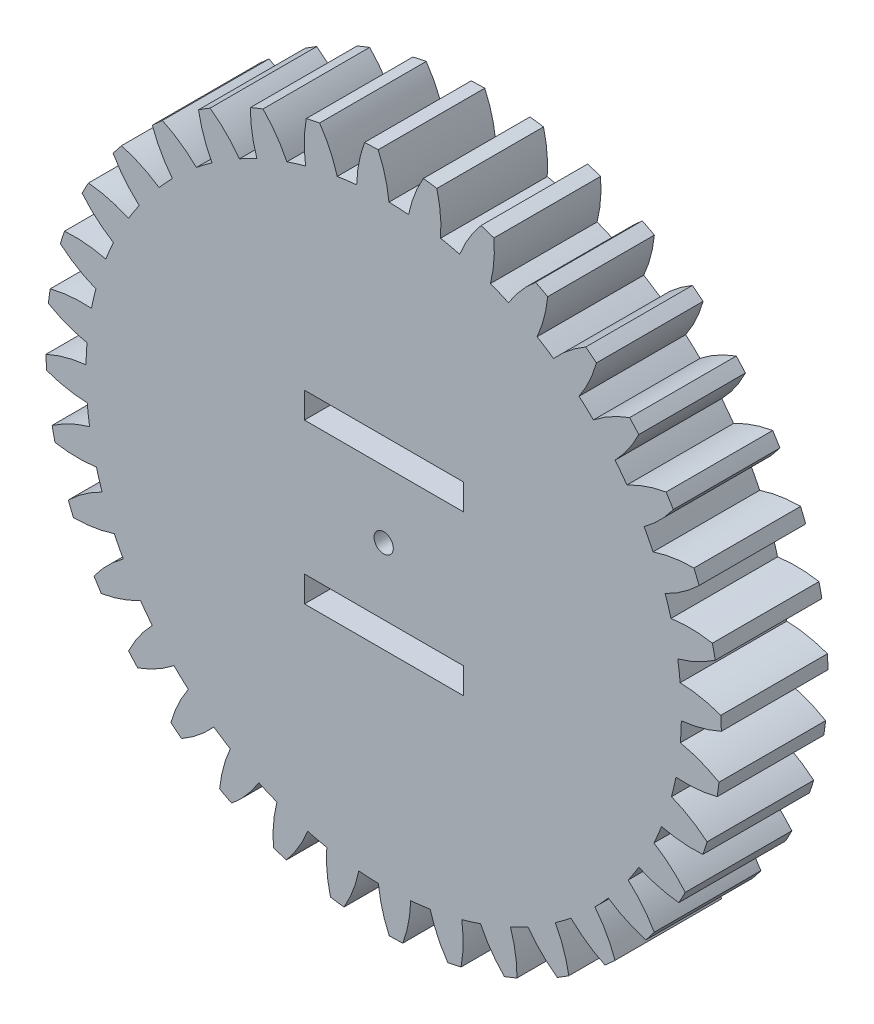
SolidWorks part; units mm, degrees
ref_plane "Front Plane" through (0, 0, 0) normal (0, 0, 1) x (1, 0, 0)
ref_plane "Top Plane" through (0, 0, 0) normal (0, 1, 0) x (1, 0, 0)
ref_plane "Right Plane" through (0, 0, 0) normal (1, 0, 0) x (0, 0, -1)
ref_plane "Plane1" through (0, 0, 0) normal (0, 0, -1) x (-1, 0, 0)
sketch "Sketch1" plane through (0, 0, 0) normal (0, 0, -1) x (-1, 0, 0)
  circle A0 centre (0, 0) radius 0.3969
  arc A1 (-79.4291, -12.6704) -> (-69.5997, -13.5532) centre (-71.8238, 16.8455) ccw
  arc A2 (-69.5997, -13.5532) -> (-68.5577, -18.1012) centre (0, 0) ccw
  arc A3 (-68.5577, -18.1012) -> (-77.0222, -23.1754) centre (-57.3249, -46.4358) ccw
  arc A4 (-77.0222, -23.1754) -> (-76.0222, -26.2707) centre (0, 0) ccw
  arc A5 (-76.0222, -26.2707) -> (-66.1889, -25.4332) centre (-73.6579, 4.1175) ccw
  arc A6 (-66.1889, -25.4332) -> (-64.3729, -29.7311) centre (0, 0) ccw
  arc A7 (-64.3729, -29.7311) -> (-71.8277, -36.1981) centre (-48.3905, -55.6847) ccw
  arc A8 (-71.8277, -36.1981) -> (-70.3054, -39.0727) centre (0, 0) ccw
  arc A9 (-70.3054, -39.0727) -> (-60.7669, -36.5404) centre (-73.2538, -8.7356) ccw
  arc A10 (-60.7669, -36.5404) -> (-58.2322, -40.4576) centre (0, 0) ccw
  arc A11 (-58.2322, -40.4576) -> (-64.4507, -48.1209) centre (-37.9858, -63.2417) ccw
  arc A12 (-64.4507, -48.1209) -> (-62.4524, -50.6875) centre (0, 0) ccw
  arc A13 (-62.4524, -50.6875) -> (-53.4985, -46.5373) centre (-70.624, -21.3233) ccw
  arc A14 (-53.4985, -46.5373) -> (-50.3221, -49.9549) centre (0, 0) ccw
  arc A15 (-50.3221, -49.9549) -> (-55.1155, -58.5816) centre (-26.4269, -68.8771) ccw
  arc A16 (-55.1155, -58.5816) -> (-52.7018, -60.7621) centre (0, 0) ccw
  arc A17 (-52.7018, -60.7621) -> (-44.6046, -55.1202) centre (-65.8483, -33.2631) ccw
  arc A18 (-44.6046, -55.1202) -> (-40.8831, -57.9343) centre (0, 0) ccw
  arc A19 (-40.8831, -57.9343) -> (-44.1056, -67.2623) centre (-14.065, -72.4197) ccw
  arc A20 (-44.1056, -67.2623) -> (-41.3499, -68.9906) centre (0, 0) ccw
  arc A21 (-41.3499, -68.9906) -> (-34.3555, -62.0283) centre (-59.0719, -44.1922) ccw
  arc A22 (-34.3555, -62.0283) -> (-30.2018, -64.1535) centre (0, 0) ccw
  arc A23 (-30.2018, -64.1535) -> (-31.7555, -73.8993) centre (-1.2758, -73.7618) ccw
  arc A24 (-31.7555, -73.8993) -> (-28.7416, -75.1228) centre (0, 0) ccw
  arc A25 (-28.7416, -75.1228) -> (-23.0624, -67.0517) centre (-50.5006, -53.7785) ccw
  arc A26 (-23.0624, -67.0517) -> (-18.6028, -68.4233) centre (0, 0) ccw
  arc A27 (-18.6028, -68.4233) -> (-18.4406, -78.2909) centre (11.5522, -72.8628) ccw
  arc A28 (-18.4406, -78.2909) -> (-15.26, -78.9725) centre (0, 0) ccw
  arc A29 (-15.26, -78.9725) -> (-11.0686, -70.0378) centre (-40.3948, -61.7308) ccw
  arc A30 (-11.0686, -70.0378) -> (-6.4386, -70.6141) centre (0, 0) ccw
  arc A31 (-6.4386, -70.6141) -> (-4.5654, -80.3037) centre (24.0291, -69.7498) ccw
  arc A32 (-4.5654, -80.3037) -> (-1.3148, -80.4226) centre (0, 0) ccw
  arc A33 (-1.3148, -80.4226) -> (1.2615, -70.8958) centre (-29.0617, -67.8075) ccw
  arc A34 (1.2615, -70.8958) -> (5.9212, -70.6594) centre (0, 0) ccw
  arc A35 (5.9212, -70.6594) -> (9.4486, -79.8764) centre (35.776, -64.5175) ccw
  arc A36 (9.4486, -79.8764) -> (12.6704, -79.4291) centre (0, 0) ccw
  arc A37 (12.6704, -79.4291) -> (13.5532, -69.5997) centre (-16.8455, -71.8238) ccw
  arc A38 (13.5532, -69.5997) -> (18.1012, -68.5577) centre (0, 0) ccw
  arc A39 (18.1012, -68.5577) -> (23.1754, -77.0222) centre (46.4358, -57.3249) ccw
  arc A40 (23.1754, -77.0222) -> (26.2707, -76.0222) centre (0, 0) ccw
  arc A41 (26.2707, -76.0222) -> (25.4332, -66.1889) centre (-4.1175, -73.6579) ccw
  arc A42 (25.4332, -66.1889) -> (29.7311, -64.3729) centre (0, 0) ccw
  arc A43 (29.7311, -64.3729) -> (36.1981, -71.8277) centre (55.6847, -48.3905) ccw
  arc A44 (36.1981, -71.8277) -> (39.0727, -70.3054) centre (0, 0) ccw
  arc A45 (39.0727, -70.3054) -> (36.5404, -60.7669) centre (8.7356, -73.2538) ccw
  arc A46 (36.5404, -60.7669) -> (40.4576, -58.2322) centre (0, 0) ccw
  arc A47 (40.4576, -58.2322) -> (48.1209, -64.4507) centre (63.2417, -37.9858) ccw
  arc A48 (48.1209, -64.4507) -> (50.6875, -62.4524) centre (0, 0) ccw
  arc A49 (50.6875, -62.4524) -> (46.5373, -53.4985) centre (21.3233, -70.624) ccw
  arc A50 (46.5373, -53.4985) -> (49.9549, -50.3221) centre (0, 0) ccw
  arc A51 (49.9549, -50.3221) -> (58.5816, -55.1155) centre (68.8771, -26.4269) ccw
  arc A52 (58.5816, -55.1155) -> (60.7621, -52.7018) centre (0, 0) ccw
  arc A53 (60.7621, -52.7018) -> (55.1202, -44.6046) centre (33.2631, -65.8483) ccw
  arc A54 (55.1202, -44.6046) -> (57.9343, -40.8831) centre (0, 0) ccw
  arc A55 (57.9343, -40.8831) -> (67.2623, -44.1056) centre (72.4197, -14.065) ccw
  arc A56 (67.2623, -44.1056) -> (68.9906, -41.3499) centre (0, 0) ccw
  arc A57 (68.9906, -41.3499) -> (62.0283, -34.3555) centre (44.1922, -59.0719) ccw
  arc A58 (62.0283, -34.3555) -> (64.1535, -30.2018) centre (0, 0) ccw
  arc A59 (64.1535, -30.2018) -> (73.8993, -31.7555) centre (73.7618, -1.2758) ccw
  arc A60 (73.8993, -31.7555) -> (75.1228, -28.7416) centre (0, 0) ccw
  arc A61 (75.1228, -28.7416) -> (67.0517, -23.0624) centre (53.7785, -50.5006) ccw
  arc A62 (67.0517, -23.0624) -> (68.4233, -18.6028) centre (0, 0) ccw
  arc A63 (68.4233, -18.6028) -> (78.2909, -18.4406) centre (72.8628, 11.5522) ccw
  arc A64 (78.2909, -18.4406) -> (78.9725, -15.26) centre (0, 0) ccw
  arc A65 (78.9725, -15.26) -> (70.0378, -11.0686) centre (61.7308, -40.3948) ccw
  arc A66 (70.0378, -11.0686) -> (70.6141, -6.4386) centre (0, 0) ccw
  arc A67 (70.6141, -6.4386) -> (80.3037, -4.5654) centre (69.7498, 24.0291) ccw
  arc A68 (80.3037, -4.5654) -> (80.4226, -1.3148) centre (0, 0) ccw
  arc A69 (80.4226, -1.3148) -> (70.8958, 1.2615) centre (67.8075, -29.0617) ccw
  arc A70 (70.8958, 1.2615) -> (70.6594, 5.9212) centre (0, 0) ccw
  arc A71 (70.6594, 5.9212) -> (79.8764, 9.4486) centre (64.5175, 35.776) ccw
  arc A72 (79.8764, 9.4486) -> (79.4291, 12.6704) centre (0, 0) ccw
  arc A73 (79.4291, 12.6704) -> (69.5997, 13.5532) centre (71.8238, -16.8455) ccw
  arc A74 (69.5997, 13.5532) -> (68.5577, 18.1012) centre (0, 0) ccw
  arc A75 (68.5577, 18.1012) -> (77.0222, 23.1754) centre (57.3249, 46.4358) ccw
  arc A76 (77.0222, 23.1754) -> (76.0222, 26.2707) centre (0, 0) ccw
  arc A77 (76.0222, 26.2707) -> (66.1889, 25.4332) centre (73.6579, -4.1175) ccw
  arc A78 (66.1889, 25.4332) -> (64.3729, 29.7311) centre (0, 0) ccw
  arc A79 (64.3729, 29.7311) -> (71.8277, 36.1981) centre (48.3905, 55.6847) ccw
  arc A80 (71.8277, 36.1981) -> (70.3054, 39.0727) centre (0, 0) ccw
  arc A81 (70.3054, 39.0727) -> (60.7669, 36.5404) centre (73.2538, 8.7356) ccw
  arc A82 (60.7669, 36.5404) -> (58.2322, 40.4576) centre (0, 0) ccw
  arc A83 (58.2322, 40.4576) -> (64.4507, 48.1209) centre (37.9858, 63.2417) ccw
  arc A84 (64.4507, 48.1209) -> (62.4524, 50.6875) centre (0, 0) ccw
  arc A85 (62.4524, 50.6875) -> (53.4985, 46.5373) centre (70.624, 21.3233) ccw
  arc A86 (53.4985, 46.5373) -> (50.3221, 49.9549) centre (0, 0) ccw
  arc A87 (50.3221, 49.9549) -> (55.1155, 58.5816) centre (26.4269, 68.8771) ccw
  arc A88 (55.1155, 58.5816) -> (52.7018, 60.7621) centre (0, 0) ccw
  arc A89 (52.7018, 60.7621) -> (44.6046, 55.1202) centre (65.8483, 33.2631) ccw
  arc A90 (44.6046, 55.1202) -> (40.8831, 57.9343) centre (0, 0) ccw
  arc A91 (40.8831, 57.9343) -> (44.1056, 67.2623) centre (14.065, 72.4197) ccw
  arc A92 (44.1056, 67.2623) -> (41.3499, 68.9906) centre (0, 0) ccw
  arc A93 (41.3499, 68.9906) -> (34.3555, 62.0283) centre (59.0719, 44.1922) ccw
  arc A94 (34.3555, 62.0283) -> (30.2018, 64.1535) centre (0, 0) ccw
  arc A95 (30.2018, 64.1535) -> (31.7555, 73.8993) centre (1.2758, 73.7618) ccw
  arc A96 (31.7555, 73.8993) -> (28.7416, 75.1228) centre (0, 0) ccw
  arc A97 (28.7416, 75.1228) -> (23.0624, 67.0517) centre (50.5006, 53.7785) ccw
  arc A98 (23.0624, 67.0517) -> (18.6028, 68.4233) centre (0, 0) ccw
  arc A99 (18.6028, 68.4233) -> (18.4406, 78.2909) centre (-11.5522, 72.8628) ccw
  arc A100 (18.4406, 78.2909) -> (15.26, 78.9725) centre (0, 0) ccw
  arc A101 (15.26, 78.9725) -> (11.0686, 70.0378) centre (40.3948, 61.7308) ccw
  arc A102 (11.0686, 70.0378) -> (6.4386, 70.6141) centre (0, 0) ccw
  arc A103 (6.4386, 70.6141) -> (4.5654, 80.3037) centre (-24.0291, 69.7498) ccw
  arc A104 (4.5654, 80.3037) -> (1.3148, 80.4226) centre (0, 0) ccw
  arc A105 (1.3148, 80.4226) -> (-1.2615, 70.8958) centre (29.0617, 67.8075) ccw
  arc A106 (-1.2615, 70.8958) -> (-5.9212, 70.6594) centre (0, 0) ccw
  arc A107 (-5.9212, 70.6594) -> (-9.4486, 79.8764) centre (-35.776, 64.5175) ccw
  arc A108 (-9.4486, 79.8764) -> (-12.6704, 79.4291) centre (0, 0) ccw
  arc A109 (-12.6704, 79.4291) -> (-13.5532, 69.5997) centre (16.8455, 71.8238) ccw
  arc A110 (-13.5532, 69.5997) -> (-18.1012, 68.5577) centre (0, 0) ccw
  arc A111 (-18.1012, 68.5577) -> (-23.1754, 77.0222) centre (-46.4358, 57.3249) ccw
  arc A112 (-23.1754, 77.0222) -> (-26.2707, 76.0222) centre (0, 0) ccw
  arc A113 (-26.2707, 76.0222) -> (-25.4332, 66.1889) centre (4.1175, 73.6579) ccw
  arc A114 (-25.4332, 66.1889) -> (-29.7311, 64.3729) centre (0, 0) ccw
  arc A115 (-29.7311, 64.3729) -> (-36.1981, 71.8277) centre (-55.6847, 48.3905) ccw
  arc A116 (-36.1981, 71.8277) -> (-39.0727, 70.3054) centre (0, 0) ccw
  arc A117 (-39.0727, 70.3054) -> (-36.5404, 60.7669) centre (-8.7356, 73.2538) ccw
  arc A118 (-36.5404, 60.7669) -> (-40.4576, 58.2322) centre (0, 0) ccw
  arc A119 (-40.4576, 58.2322) -> (-48.1209, 64.4507) centre (-63.2417, 37.9858) ccw
  arc A120 (-48.1209, 64.4507) -> (-50.6875, 62.4524) centre (0, 0) ccw
  arc A121 (-50.6875, 62.4524) -> (-46.5373, 53.4985) centre (-21.3233, 70.624) ccw
  arc A122 (-46.5373, 53.4985) -> (-49.9549, 50.3221) centre (0, 0) ccw
  arc A123 (-49.9549, 50.3221) -> (-58.5816, 55.1155) centre (-68.8771, 26.4269) ccw
  arc A124 (-58.5816, 55.1155) -> (-60.7621, 52.7018) centre (0, 0) ccw
  arc A125 (-60.7621, 52.7018) -> (-55.1202, 44.6046) centre (-33.2631, 65.8483) ccw
  arc A126 (-55.1202, 44.6046) -> (-57.9343, 40.8831) centre (0, 0) ccw
  arc A127 (-57.9343, 40.8831) -> (-67.2623, 44.1056) centre (-72.4197, 14.065) ccw
  arc A128 (-67.2623, 44.1056) -> (-68.9906, 41.3499) centre (0, 0) ccw
  arc A129 (-68.9906, 41.3499) -> (-62.0283, 34.3555) centre (-44.1922, 59.0719) ccw
  arc A130 (-62.0283, 34.3555) -> (-64.1535, 30.2018) centre (0, 0) ccw
  arc A131 (-64.1535, 30.2018) -> (-73.8993, 31.7555) centre (-73.7618, 1.2758) ccw
  arc A132 (-73.8993, 31.7555) -> (-75.1228, 28.7416) centre (0, 0) ccw
  arc A133 (-75.1228, 28.7416) -> (-67.0517, 23.0624) centre (-53.7785, 50.5006) ccw
  arc A134 (-67.0517, 23.0624) -> (-68.4233, 18.6028) centre (0, 0) ccw
  arc A135 (-68.4233, 18.6028) -> (-78.2909, 18.4406) centre (-72.8628, -11.5522) ccw
  arc A136 (-78.2909, 18.4406) -> (-78.9725, 15.26) centre (0, 0) ccw
  arc A137 (-78.9725, 15.26) -> (-70.0378, 11.0686) centre (-61.7308, 40.3948) ccw
  arc A138 (-70.0378, 11.0686) -> (-70.6141, 6.4386) centre (0, 0) ccw
  arc A139 (-70.6141, 6.4386) -> (-80.3037, 4.5654) centre (-69.7498, -24.0291) ccw
  arc A140 (-80.3037, 4.5654) -> (-80.4226, 1.3148) centre (0, 0) ccw
  arc A141 (-80.4226, 1.3148) -> (-70.8958, -1.2615) centre (-67.8075, 29.0617) ccw
  arc A142 (-70.8958, -1.2615) -> (-70.6594, -5.9212) centre (0, 0) ccw
  arc A143 (-70.6594, -5.9212) -> (-79.8764, -9.4486) centre (-64.5175, -35.776) ccw
  arc A144 (-79.8764, -9.4486) -> (-79.4291, -12.6704) centre (0, 0) ccw
extrude "Boss-Extrude1" add sketch "Sketch1" against normal blind 25.4
sketch "Sketch2" plane through (0, 0, 25.4) normal (0, 0, 1) x (1, 0, 0)
  line L1 (19.05, 15.875) -> (-18.8722, 15.875)
  line L2 (19.05, 22.0472) -> (-18.8722, 22.0472)
  line L3 (19.05, 22.0472) -> (19.05, 15.875)
  line L4 (-31.2552, 0) -> (65.7215, 0) construction
  line L5 (-18.8722, 22.0472) -> (-18.8722, 15.875)
  line L10 (-18.8722, -22.0472) -> (-18.8722, -15.875)
  line L11 (19.05, -22.0472) -> (19.05, -15.875)
  line L12 (19.05, -22.0472) -> (-18.8722, -22.0472)
  line L13 (19.05, -15.875) -> (-18.8722, -15.875)
  circle A0 centre (0, 0) radius 2.2924
  point P6 (0, 0)
  point P13 (0.0889, 15.875)
  point P17 (0.0889, -15.875)
  dimension "D1" = 4.5847
  dimension "D2" = 31.75
  dimension "D3" = 37.9222
  dimension "D4" = 6.1722
extrude "Cut-Extrude1" cut sketch "Sketch2" against normal through all
